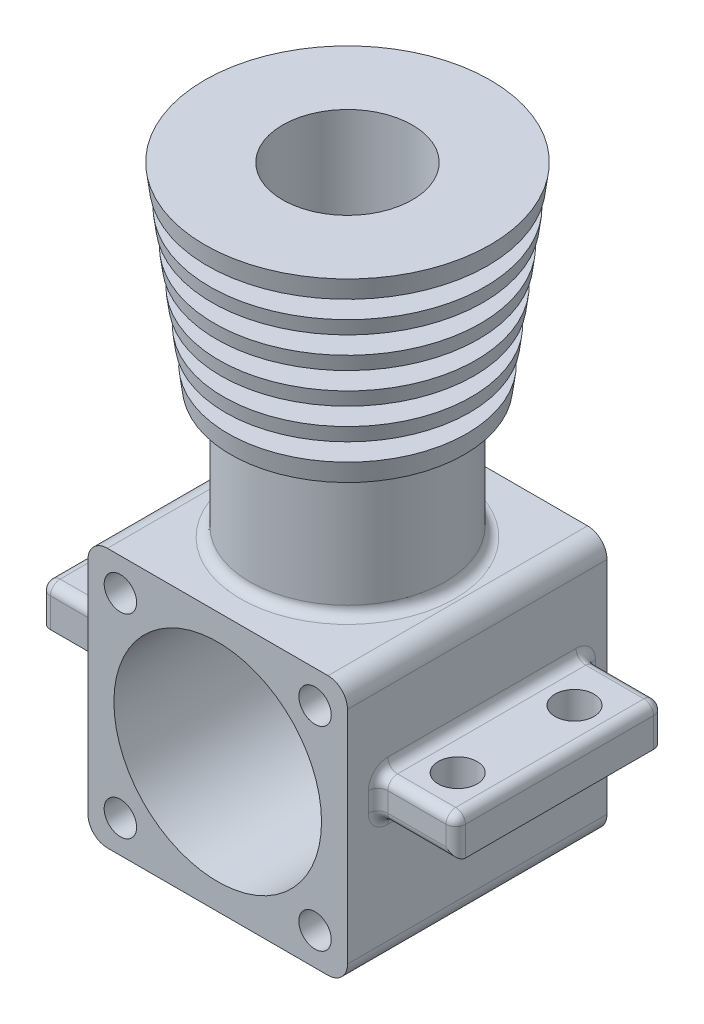
SolidWorks part; units mm, degrees
ref_plane "Front Plane" through (0, 0, 0) normal (0, 0, 1) x (1, 0, 0)
ref_plane "Top Plane" through (0, 0, 0) normal (0, 1, 0) x (1, 0, 0)
ref_plane "Right Plane" through (0, 0, 0) normal (1, 0, 0) x (0, 0, -1)
sketch "Sketch1" plane through (0, 0, 0) normal (0, 0, 1) x (1, 0, 0)
  line L1 (-19.9823, 19.9654) -> (20.0177, 19.9654)
  line L2 (-19.9823, 19.9654) -> (-19.9823, -20.0346)
  line L3 (-19.9823, -20.0346) -> (20.0177, -20.0346)
  line L4 (20.0177, 19.9654) -> (20.0177, -20.0346)
  line L5 (-19.9823, 19.9654) -> (20.0177, -20.0346) construction
  line L6 (-19.9823, -20.0346) -> (20.0177, 19.9654) construction
  line L7 (-14.9823, 14.9654) -> (15.0177, 14.9654) construction
  line L8 (-14.9823, 14.9654) -> (-14.9823, -15.0346) construction
  line L9 (-14.9823, -15.0346) -> (15.0177, -15.0346) construction
  line L10 (15.0177, 14.9654) -> (15.0177, -15.0346) construction
  line L11 (-14.9823, 14.9654) -> (15.0177, -15.0346) construction
  line L12 (-14.9823, -15.0346) -> (15.0177, 14.9654) construction
  circle A0 centre (-14.9823, 14.9654) radius 2.5
  circle A1 centre (15.0177, 14.9654) radius 2.5
  circle A2 centre (15.0177, -15.0346) radius 2.5
  circle A3 centre (-14.9823, -15.0346) radius 2.5
  circle A4 centre (0.0177, -0.0346) radius 16
  point P0 (0.0177, -0.0346)
  point P7 (0.0177, -0.0346)
  dimension "D4" = 5
  dimension "D5" = 32
  dimension "D1" = 40
  dimension "D2" = 40
  dimension "D3" = 5
extrude "Boss-Extrude1" add sketch "Sketch1" along normal mid plane 40
fillet "Fillet2" radius 3 4 edges at (20.0177, -20.0346, 0) (-19.9823, -20.0346, 0) (20.0177, 19.9654, 0) (-19.9823, 19.9654, 0)
sketch "Sketch2" plane through (0, 0, 0) normal (0, 0, 1) x (1, 0, 0)
  line L0 (0.0177, 19.9654) -> (0.0177, 69.9654)
  line L1 (17.0177, 19.9654) -> (-16.9823, 19.9654) construction
  line L2 (0.0177, 69.9654) -> (-21.9823, 69.9654)
  line L3 (-21.9823, 69.9654) -> (-17.9823, 39.9654)
  line L4 (-17.9823, 39.9654) -> (-14.9823, 39.9654)
  line L5 (-14.9823, 39.9654) -> (-14.9823, 19.9654)
  line L6 (-14.9823, 19.9654) -> (0.0177, 19.9654)
  point P4 (-14.9823, 29.9654)
  dimension "D1" = 22
  dimension "D2" = 50
  dimension "D3" = 15
  dimension "D4" = 20
  dimension "D5" = 18
revolve "Revolve2" add sketch "Sketch2" angle 360 about L0
sketch "Sketch7" plane through (0, 0, 0) normal (0, 0, 1) x (1, 0, 0)
  line L0 (-29.9823, 45.9654) -> (-11.9823, 45.9654)
  line L1 (-11.9823, 45.9654) -> (-11.9823, 42.9654)
  line L2 (-11.9823, 42.9654) -> (-29.9823, 42.9654)
  line L3 (-29.9823, 42.9654) -> (-29.9823, 45.9654)
  line L4 (-17.9823, 39.9654) -> (18.0177, 39.9654) construction
  line L5 (0.0177, -20.0346) -> (0.0177, 42.9654) construction
  line L6 (-16.9823, -20.0346) -> (17.0177, -20.0346) construction
  line L8 (0.0177, 42.9654) -> (0.0177, 69.9654) construction
  line L9 (22.0177, 69.9654) -> (-21.9823, 69.9654) construction
  dimension "D1" = 3
  dimension "D2" = 3
  dimension "D3" = 30
  dimension "D4" = 12
revolve "Cut-Revolve3" cut sketch "Sketch7" angle 360 about L8
pattern_linear "LPattern1" count 5 spacing 5.25 along (0, 1, 0) of "Cut-Revolve3"
sketch "Sketch8" plane through (0, 69.9654, 0) normal (0, 1, 0) x (1, 0, 0)
  circle A0 centre (0.0177, 0) radius 10
  dimension "D1" = 20
extrude "Cut-Extrude1" cut sketch "Sketch8" against normal blind 70 contours A0
sketch "Sketch10" plane through (0, 0, 0) normal (0, 1, 0) x (1, 0, 0)
  line L1 (-19.9823, -20) -> (-19.9823, 20) construction
  line L4 (-19.9823, -15.2872) -> (-19.9823, 16.7128)
  line L5 (0, 29.92) -> (0, -33.2651) construction
  line L7 (-19.9823, 16.7128) -> (-31.9823, 16.7128)
  line L8 (-31.9823, 16.7128) -> (-31.9823, -15.2872)
  line L9 (-31.9823, -15.2872) -> (-19.9823, -15.2872)
  line L10 (-19.9823, 16.7128) -> (-19.9823, -15.2872)
  circle A0 centre (-26, 9) radius 3
  circle A1 centre (-26, -9) radius 3
  dimension "D5" = 6
  dimension "D1" = 18
  dimension "D2" = 12
  dimension "D3" = 32
  dimension "D4" = 26
extrude "Boss-Extrude2" add sketch "Sketch10" along normal blind 6 contours L8 L9 L4 L7 A1 A0
mirror "Mirror1" about plane through (0, 0, 0) normal (1, 0, 0) of "Boss-Extrude2"
fillet "Fillet4" radius 1.5 19 edges at (20.0177, 0, -0.7128) (20.0177, 6, -0.7128) (20.0177, 3, 15.2872) (26, 0, 15.2872) (20.0177, 3, -16.7128) (31.9823, 3, 15.2872) (31.9823, 3, -16.7128) (26, 6, -16.7128) (31.9823, 6, -0.7128) (26, 6, 15.2872) (15.0177, 19.9654, 0) (-19.9823, 6, -0.7128) (-19.9823, 3, -16.7128) (-31.9823, 3, -16.7128) (-19.9823, 3, 15.2872) (-31.9823, 3, 15.2872) (-25.9823, 6, -16.7128) (-25.9823, 6, 15.2872) (-31.9823, 6, -0.7128)
